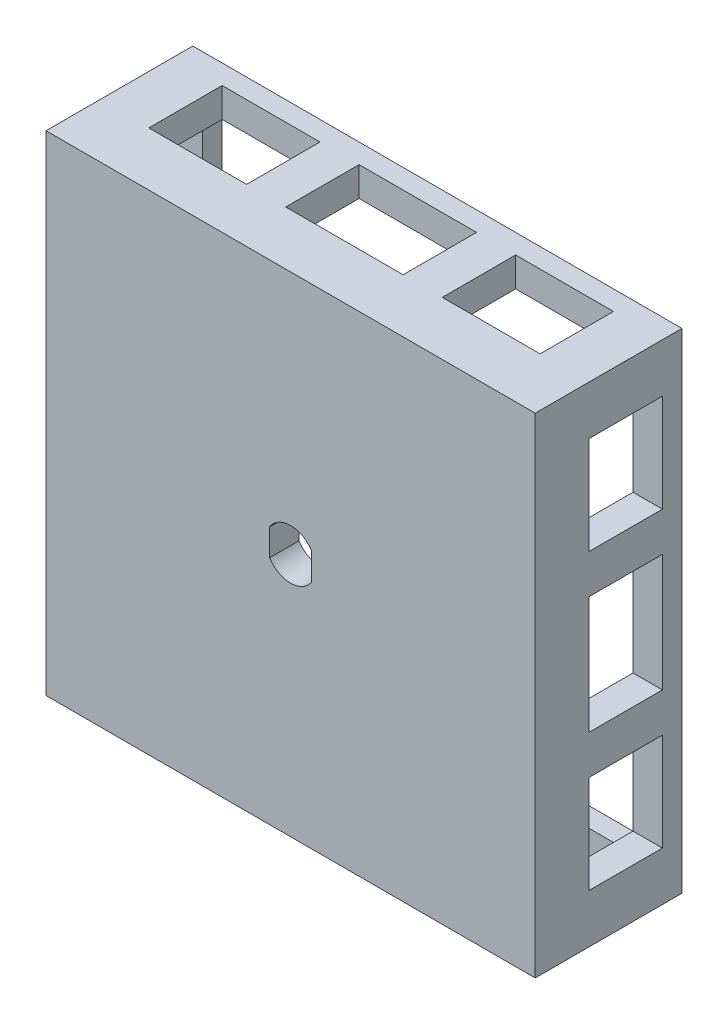
SolidWorks part; units mm, degrees
other "Markup1"
sketch "Sketch7" plane through (-25, 25, 0) normal (-0.8653, 0.4997, -0.0379) x (0.444, 0.7995, 0.4046)
ref_plane "Front Plane" through (0, 0, 0) normal (0, 0, 1) x (1, 0, 0)
ref_plane "Top Plane" through (0, 0, 0) normal (0, 1, 0) x (1, 0, 0)
ref_plane "Right Plane" through (0, 0, 0) normal (1, 0, 0) x (0, 0, -1)
sketch "Sketch1" plane through (0, 0, 0) normal (0, 0, 1) x (1, 0, 0)
  line L1 (-25, -25) -> (25, -25)
  line L2 (-25, -25) -> (-25, 25)
  line L3 (-25, 25) -> (25, 25)
  line L4 (25, -25) -> (25, 25)
  line L5 (-25, -25) -> (25, 25) construction
  line L6 (-25, 25) -> (25, -25) construction
  point P0 (0, 0)
  dimension "D1" = 50
  dimension "D2" = 50
extrude "Boss-Extrude1" add sketch "Sketch1" along normal blind 15
shell "Shell1" thickness 3
sketch "Sketch2" plane through (0, 0, 0) normal (0, 0, -1) x (-1, 0, 0)
  line L0 (0, 2.55) -> (0, -2.55) construction
  line L1 (-2.15, 1.3711) -> (-2.15, -1.3711)
  line L2 (2.15, 1.3711) -> (2.15, -1.3711)
  arc A0 (-2.15, -1.3711) -> (2.15, -1.3711) centre (0, 0) ccw
  arc A1 (-2.15, 1.3711) -> (-2.15, -1.3711) centre (0, 0) ccw construction
  arc A2 (2.15, 1.3711) -> (-2.15, 1.3711) centre (0, 0) ccw
  arc A3 (2.15, -1.3711) -> (2.15, 1.3711) centre (0, 0) ccw construction
  dimension "D1" = 5.1
  dimension "D2" = 2.15
extrude "Cut-Extrude1" cut sketch "Sketch2" against normal through all both and the other way through all
sketch "Sketch4" plane through (0, 0, 0) normal (0, 0, -1) x (-1, 0, 0)
  line L0 (-17.5, 17.5) -> (-17.5, 27.9484)
  line L1 (26.9415, -17.5) -> (17.5, -17.5)
  line L2 (26.9415, -17.5) -> (26.9415, 17.5)
  line L3 (26.9415, 17.5) -> (17.5, 17.5)
  line L4 (-26.9415, -17.5) -> (-26.9415, 17.5)
  line L5 (26.9415, -17.5) -> (-26.9415, 17.5) construction
  line L6 (26.9415, 17.5) -> (-26.9415, -17.5) construction
  line L7 (17.5, -27.9484) -> (-17.5, -27.9484)
  line L8 (17.5, -27.9484) -> (17.5, -17.5)
  line L9 (17.5, 27.9484) -> (-17.5, 27.9484)
  line L10 (-17.5, -27.9484) -> (-17.5, -17.5)
  line L11 (17.5, -27.9484) -> (-17.5, 27.9484) construction
  line L12 (17.5, 27.9484) -> (-17.5, -27.9484) construction
  line L13 (-17.5, 11.3672) -> (-17.5, 17.5) construction
  line L14 (-17.5, -11.3672) -> (-17.5, 11.3672) construction
  line L15 (-17.5, -17.5) -> (-17.5, -11.3672) construction
  line L16 (-17.5, -17.5) -> (-26.9415, -17.5)
  line L17 (-10.9577, -17.5) -> (-17.5, -17.5) construction
  line L18 (10.9577, -17.5) -> (-10.9577, -17.5) construction
  line L19 (17.5, -17.5) -> (10.9577, -17.5) construction
  line L20 (17.5, 17.5) -> (17.5, 27.9484)
  line L21 (17.5, -17.5) -> (17.5, -11.3672) construction
  line L22 (17.5, -11.3672) -> (17.5, 11.3672) construction
  line L23 (17.5, 11.3672) -> (17.5, 17.5) construction
  line L24 (-17.5, 17.5) -> (-26.9415, 17.5)
  line L25 (17.5, 17.5) -> (10.9577, 17.5) construction
  line L26 (10.9577, 17.5) -> (-10.9577, 17.5) construction
  line L27 (-10.9577, 17.5) -> (-17.5, 17.5) construction
  point P0 (0, 0)
  point P6 (0, 0)
  dimension "D1" = 35
  dimension "D2" = 35
sketch "Sketch5" plane through (-25, 0, 0) normal (-1, 0, 0) x (0, 0, 1)
  line L8 (7.5, 25) -> (7.5, -25) construction
  line L13 (15, 25) -> (0, 25) construction
  line L14 (15, -25) -> (0, -25) construction
  line L19 (0, 0) -> (15, 0) construction
  line L20 (0, -11.3672) -> (0, 11.3672) construction
  line L25 (15, 25) -> (15, -25) construction
  line L28 (2, 10) -> (9.5, 10)
  line L29 (2, 10) -> (2, 20)
  line L30 (2, 20) -> (9.5, 20)
  line L31 (9.5, 10) -> (9.5, 20)
  line L32 (2, 10) -> (9.5, 20) construction
  line L33 (2, 20) -> (9.5, 10) construction
  line L34 (2, -6) -> (9.5, -6)
  line L35 (2, -6) -> (2, 6)
  line L36 (2, 6) -> (9.5, 6)
  line L37 (9.5, -6) -> (9.5, 6)
  line L38 (2, -6) -> (9.5, 6) construction
  line L39 (2, 6) -> (9.5, -6) construction
  line L40 (2, -20) -> (9.5, -20)
  line L41 (2, -20) -> (2, -10)
  line L42 (2, -10) -> (9.5, -10)
  line L43 (9.5, -20) -> (9.5, -10)
  line L44 (2, -20) -> (9.5, -10) construction
  line L45 (2, -10) -> (9.5, -20) construction
  line L46 (12, 22) -> (12, -22) construction
  point P14 (5.75, 15)
  point P19 (5.75, 0)
  point P24 (5.75, -15)
  dimension "D1" = 2.5
  dimension "D2" = 10
  dimension "D3" = 12
  dimension "D4" = 10
  dimension "D5" = 2.5
  dimension "D6" = 2.5
  dimension "D7" = 7.5
  dimension "D8" = 7.5
  dimension "D9" = 7.5
  dimension "D10" = 10
  dimension "D11" = 10
extrude "Cut-Extrude2" cut sketch "Sketch5" against normal through all both and the other way through all
sketch "Sketch6" plane through (0, -25, 0) normal (0, -1, 0) x (1, 0, 0)
  line L0 (-25, 7.5) -> (25, 7.5) construction
  line L1 (-25, 15) -> (-25, 0) construction
  line L2 (25, 15) -> (25, 0) construction
  line L3 (0, 0) -> (0, 15) construction
  line L4 (-10.9577, 0) -> (10.9577, 0) construction
  line L5 (-25, 15) -> (25, 15) construction
  line L6 (-22, 12) -> (22, 12) construction
  line L7 (-6, 2) -> (6, 2)
  line L8 (-6, 2) -> (-6, 9.5)
  line L9 (-6, 9.5) -> (6, 9.5)
  line L10 (6, 2) -> (6, 9.5)
  line L11 (-6, 2) -> (6, 9.5) construction
  line L12 (-6, 9.5) -> (6, 2) construction
  line L13 (10, 9.5) -> (20, 9.5)
  line L14 (10, 9.5) -> (10, 2)
  line L15 (10, 2) -> (20, 2)
  line L16 (20, 9.5) -> (20, 2)
  line L17 (10, 9.5) -> (20, 2) construction
  line L18 (10, 2) -> (20, 9.5) construction
  line L19 (-20, 9.5) -> (-10, 9.5)
  line L20 (-20, 9.5) -> (-20, 2)
  line L21 (-20, 2) -> (-10, 2)
  line L22 (-10, 9.5) -> (-10, 2)
  line L23 (-20, 9.5) -> (-10, 2) construction
  line L24 (-20, 2) -> (-10, 9.5) construction
  point P12 (0, 5.75)
  point P17 (15, 5.75)
  point P22 (-15, 5.75)
  dimension "D1" = 10
  dimension "D2" = 12
  dimension "D3" = 10
  dimension "D4" = 10
  dimension "D5" = 10
  dimension "D6" = 2.5
  dimension "D7" = 2.5
  dimension "D8" = 2.5
  dimension "D9" = 7.5
  dimension "D10" = 7.5
  dimension "D11" = 7.5
extrude "Cut-Extrude3" cut sketch "Sketch6" against normal through all both and the other way through all
